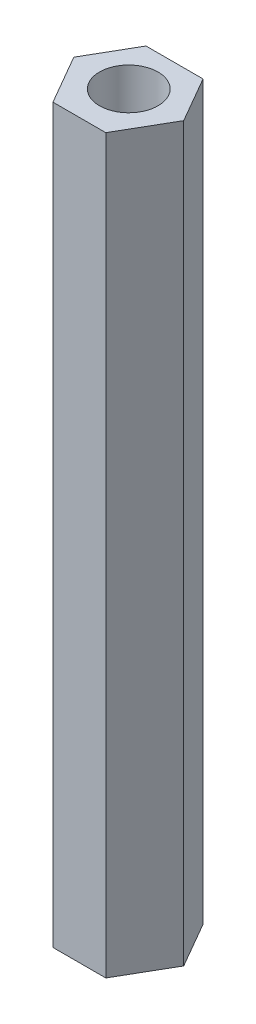
SolidWorks part; units mm, degrees
ref_plane "前视基准面" through (0, 0, 0) normal (0, 0, 1) x (1, 0, 0)
ref_plane "上视基准面" through (0, 0, 0) normal (0, 1, 0) x (1, 0, 0)
ref_plane "右视基准面" through (0, 0, 0) normal (1, 0, 0) x (0, 0, -1)
sketch "草图1" plane through (0, 0, 0) normal (0, 1, 0) x (1, 0, 0)
  line L0 (-3.0004, 5.3056) -> (4.7906, 5.3056)
  line L1 (4.7906, 5.3056) -> (8.4006, -0.9472)
  line L2 (8.4006, -0.9472) -> (4.5051, -7.6944)
  line L3 (4.5051, -7.6944) -> (-2.7149, -7.6944)
  line L4 (-2.7149, -7.6944) -> (-6.6105, -0.9472)
  line L5 (-6.6105, -0.9472) -> (-3.0004, 5.3056)
  line L6 (0.8951, 5.3056) -> (0.8951, -7.6944) construction
  line L7 (8.4006, -0.9472) -> (-6.6105, -0.9472) construction
  circle A0 centre (0.8951, -0.9472) radius 4
  dimension "D6" = 8
  dimension "D1" = 13
  dimension "D2" = 13
  dimension "D3" = 13
  dimension "D4" = 120
  dimension "D5" = 120
extrude "凸台-拉伸1" add sketch "草图1" along normal blind 100
